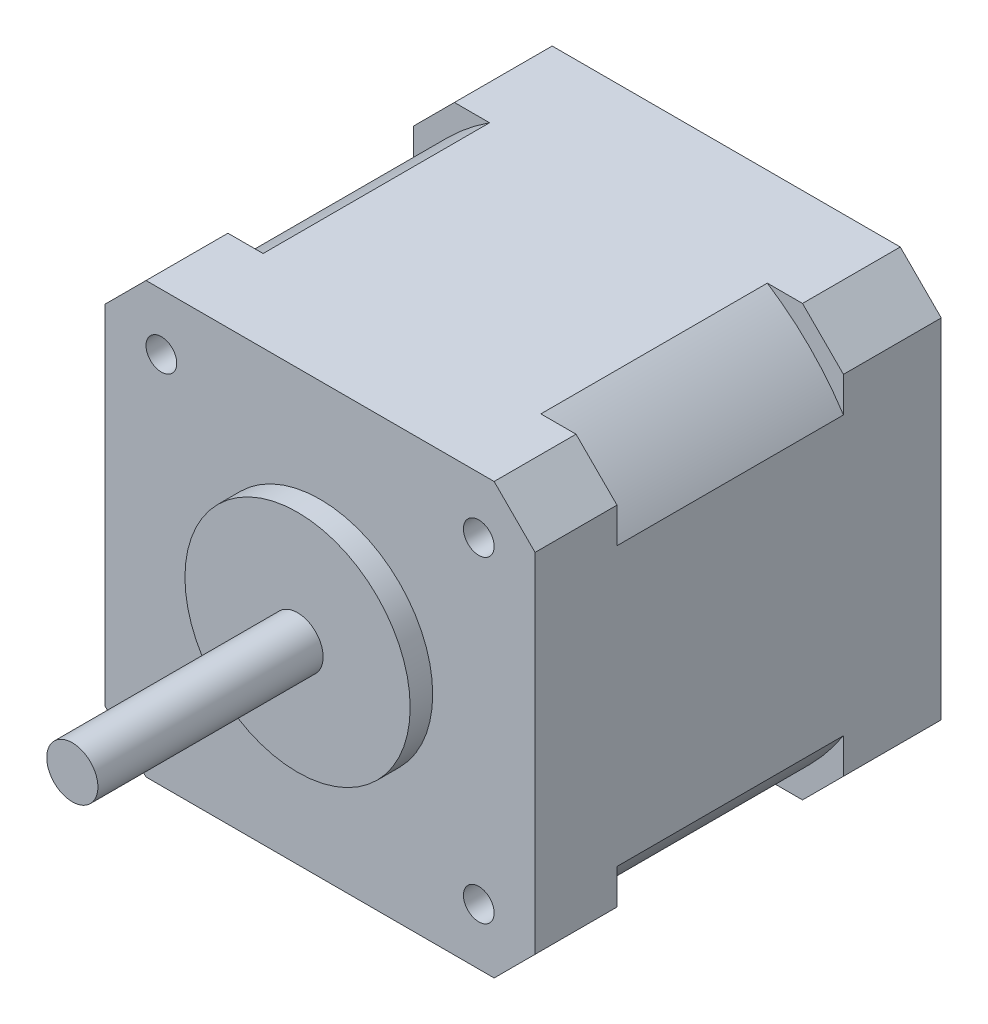
SolidWorks part; units mm, degrees
ref_plane "Front Plane" through (0, 0, 0) normal (0, 0, 1) x (1, 0, 0)
ref_plane "Top Plane" through (0, 0, 0) normal (0, 1, 0) x (1, 0, 0)
ref_plane "Right Plane" through (0, 0, 0) normal (1, 0, 0) x (0, 0, -1)
sketch "Sketch1" plane through (0, 0, 0) normal (0, 0, 1) x (1, 0, 0)
  line L8 (17, -21) -> (21, -17)
  line L9 (21, -17) -> (21, 17)
  line L10 (21, 17) -> (17, 21)
  line L11 (17, 21) -> (-17, 21)
  line L12 (-17, 21) -> (-21, 17)
  line L13 (-21, 17) -> (-21, -17)
  line L14 (-21, -17) -> (-17, -21)
  line L15 (-17, -21) -> (17, -21)
  line L16 (17, -21) -> (21, -17)
  line L17 (21, -17) -> (21, 17)
  line L18 (21, 17) -> (17, 21)
  line L19 (17, 21) -> (-17, 21)
  line L20 (-17, 21) -> (-21, 17)
  line L21 (-21, 17) -> (-21, -17)
  line L22 (-21, -17) -> (-17, -21)
  line L23 (-17, -21) -> (17, -21)
  dimension "D1" = 0
extrude "Boss-Extrude1" add sketch "Sketch1" against normal up to surface (39.67 mm away)
ref_plane "Plane1" through (0, 0, -30.12) normal (0, 0, 1) x (1, 0, 0)
sketch "Sketch2" plane through (0, 0, -30.12) normal (0, 0, 1) x (1, 0, 0)
  circle A0 centre (0, 0) radius 25
  dimension "D1" = 50
extrude "Cut-Extrude1" cut sketch "Sketch2" along normal up to vertex (22.12 mm away) flip side to cut
sketch "Sketch3" plane through (0, 0, -39.67) normal (0, 0, -1) x (-1, 0, 0)
  line L8 (-17, -21) -> (17, -21)
  line L9 (17, -21) -> (21, -17)
  line L10 (21, -17) -> (21, 17)
  line L11 (21, 17) -> (17, 21)
  line L12 (17, 21) -> (-17, 21)
  line L13 (-17, 21) -> (-21, 17)
  line L14 (-21, 17) -> (-21, -17)
  line L15 (-21, -17) -> (-17, -21)
  line L16 (-17, -21) -> (17, -21)
  line L17 (17, -21) -> (21, -17)
  line L18 (21, -17) -> (21, 17)
  line L19 (21, 17) -> (17, 21)
  line L20 (17, 21) -> (-17, 21)
  line L21 (-17, 21) -> (-21, 17)
  line L22 (-21, 17) -> (-21, -17)
  line L23 (-21, -17) -> (-17, -21)
  circle A0 centre (0, 0) radius 4.75 construction
  circle A1 centre (0, 0) radius 4.75
  circle A2 centre (15.5, 15.5) radius 1.5 construction
  circle A3 centre (15.5, 15.5) radius 1.5
  circle A4 centre (15.5, -15.5) radius 1.5 construction
  circle A5 centre (15.5, -15.5) radius 1.5
  circle A6 centre (-15.5, -15.5) radius 1.5 construction
  circle A7 centre (-15.5, -15.5) radius 1.5
  circle A8 centre (-15.5, 15.5) radius 1.5 construction
  circle A9 centre (-15.5, 15.5) radius 1.5
  dimension "D1" = 0
extrude "Cut-Extrude2" cut sketch "Sketch3" against normal blind 5 contours A3 | A5 | A9 | A7
sketch "Sketch4" plane through (0, 0, -39.67) normal (0, 0, -1) x (-1, 0, 0)
  circle A0 centre (0, 0) radius 4.75 construction
  circle A1 centre (0, 0) radius 4.75
extrude "Cut-Extrude3" cut sketch "Sketch4" against normal blind 2
sketch "Sketch5" plane through (0, 0, 0) normal (0, 0, 1) x (1, 0, 0)
  line L8 (17, -21) -> (21, -17)
  line L9 (21, -17) -> (21, 17)
  line L10 (21, 17) -> (17, 21)
  line L11 (17, 21) -> (-17, 21)
  line L12 (-17, 21) -> (-21, 17)
  line L13 (-21, 17) -> (-21, -17)
  line L14 (-21, -17) -> (-17, -21)
  line L15 (-17, -21) -> (17, -21)
  line L16 (17, -21) -> (21, -17)
  line L17 (21, -17) -> (21, 17)
  line L18 (21, 17) -> (17, 21)
  line L19 (17, 21) -> (-17, 21)
  line L20 (-17, 21) -> (-21, 17)
  line L21 (-21, 17) -> (-21, -17)
  line L22 (-21, -17) -> (-17, -21)
  line L23 (-17, -21) -> (17, -21)
  circle A0 centre (15.5, 15.5) radius 1.5 construction
  circle A1 centre (-15.5, 15.5) radius 1.5 construction
  circle A2 centre (-15.5, -15.5) radius 1.5 construction
  circle A3 centre (15.5, -15.5) radius 1.5 construction
  circle A4 centre (15.5, 15.5) radius 1.5
  circle A5 centre (-15.5, 15.5) radius 1.5
  circle A6 centre (-15.5, -15.5) radius 1.5
  circle A7 centre (15.5, -15.5) radius 1.5
  dimension "D1" = 0
extrude "Cut-Extrude4" cut sketch "Sketch5" against normal blind 5 contours A7 | A6 | A5 | A4
sketch "Sketch6" plane through (0, 0, 0) normal (0, 0, 1) x (1, 0, 0)
  circle A0 centre (0, 0) radius 11 construction
  circle A1 centre (0, 0) radius 11
extrude "Boss-Extrude2" add sketch "Sketch6" along normal blind 2.2 separate body
sketch "Sketch8" plane through (0, 0, 2.2) normal (0, 0, 1) x (1, 0, 0)
  circle A0 centre (0, 0) radius 2.5 construction
  circle A1 centre (0, 0) radius 2.5
extrude "Boss-Extrude3" add sketch "Sketch8" along normal up to surface (22 mm away)
